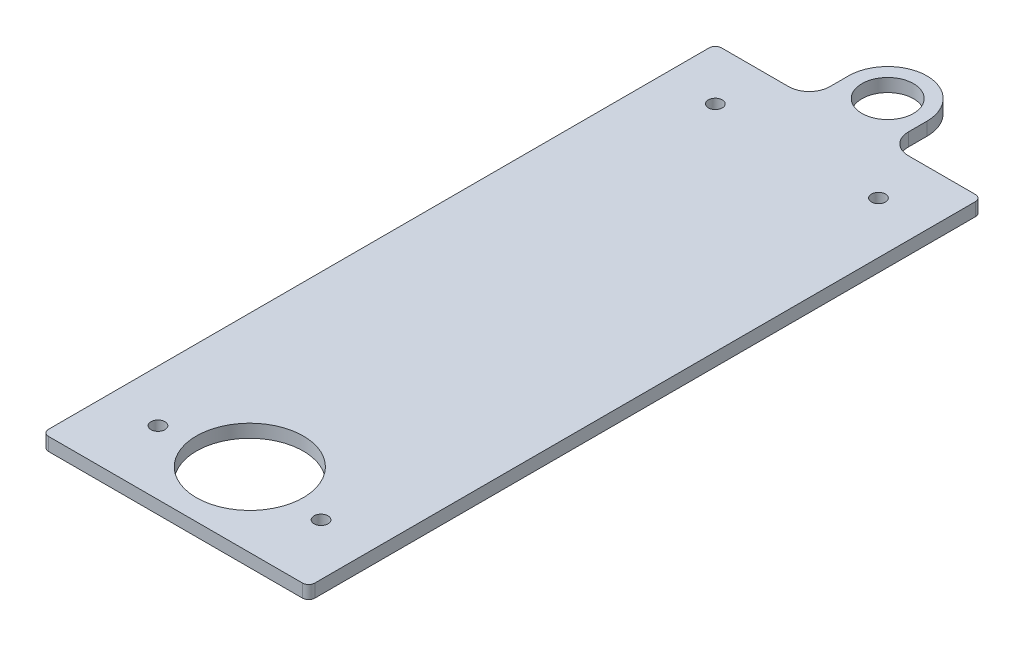
SolidWorks part; units mm, degrees
material "6061-T6 (SS)"
ref_plane "Front Plane" through (0, 0, 0) normal (0, 0, 1) x (1, 0, 0)
ref_plane "Top Plane" through (0, 0, 0) normal (0, 1, 0) x (1, 0, 0)
ref_plane "Right Plane" through (0, 0, 0) normal (1, 0, 0) x (0, 0, -1)
sketch "Sketch1" plane through (0, 0, 0) normal (0, 1, 0) x (1, 0, 0)
  line L0 (0, 0) -> (0, 84.7264) construction
  line L1 (-64.5, 160) -> (-19, 160)
  line L2 (-64.5, 160) -> (-64.5, -166)
  line L3 (-64.5, -166) -> (64.5, -166)
  line L4 (64.5, 160) -> (64.5, -166)
  line L5 (0, 0) -> (48.7831, 0) construction
  line L6 (-64.5, -160) -> (64.5, -160) construction
  line L7 (19, 160) -> (64.5, 160)
  line L9 (19, 160) -> (19, 179)
  line L11 (-19, 160) -> (-19, 179)
  circle A0 centre (0, -130) radius 25.9
  arc A1 (19, 179) -> (-19, 179) centre (0, 179) ccw
  circle A2 centre (0, 179) radius 12.5
  point P0 (0, 0)
  point P10 (0, -166)
  dimension "D3" = 51.8
  dimension "D7" = 25
  dimension "D1" = 129
  dimension "D2" = 326
  dimension "D4" = 130
  dimension "D5" = 160
  dimension "D6" = 38
  dimension "D8" = 19
extrude "Boss-Extrude1" add sketch "Sketch1" along normal blind 6.35
hole_wizard "1/4 Clearance Hole1" positions "Sketch3" profile "Sketch2" hole size "1/4" standard "ANSI Inch"
sketch "Sketch3" plane through (0, 6.35, 0) normal (0, 1, 0) x (1, 0, 0)
  line L0 (0, 0) -> (0, 38.785) construction
  line L1 (0, 0) -> (39.9507, 0) construction
  line L2 (-19, 160) -> (-64.5, 160) construction
  line L3 (-64.5, 160) -> (-64.5, -166) construction
  circle A0 centre (-39.5, 135) radius 25 construction
  point P0 (-39.5, 135)
  point P17 (39.5, 135)
  point P18 (39.5, -135)
  point P19 (-39.5, -135)
  dimension "D1" = 50
sketch "Sketch2" plane through (-39.5, 6.35, -135) normal (1, 0, 0) x (0, 0, 1)
  line L0 (0, 0) -> (0, 21.5598)
  line L1 (0, 21.5598) -> (3.3782, 19.53)
  line L2 (3.3782, 19.53) -> (3.3782, 0)
  line L5 (3.3782, 0) -> (0, 0)
  line L10 (0, 21.5598) -> (-3.3782, 19.53) construction
  line L11 (0, -6.35) -> (0, 107.95) construction
  dimension "Hole Dia." = 6.7564
  dimension "Hole Depth" = 19.53
  dimension "Drill Angle" = 118
fillet "Fillet1" radius 10 2 edges at (-19, 3.175, -160) (19, 3.175, -160)
fillet "Fillet2" radius 3 4 edges at (64.5, 3.175, 166) (-64.5, 3.175, 166) (64.5, 3.175, -160) (-64.5, 3.175, -160)
